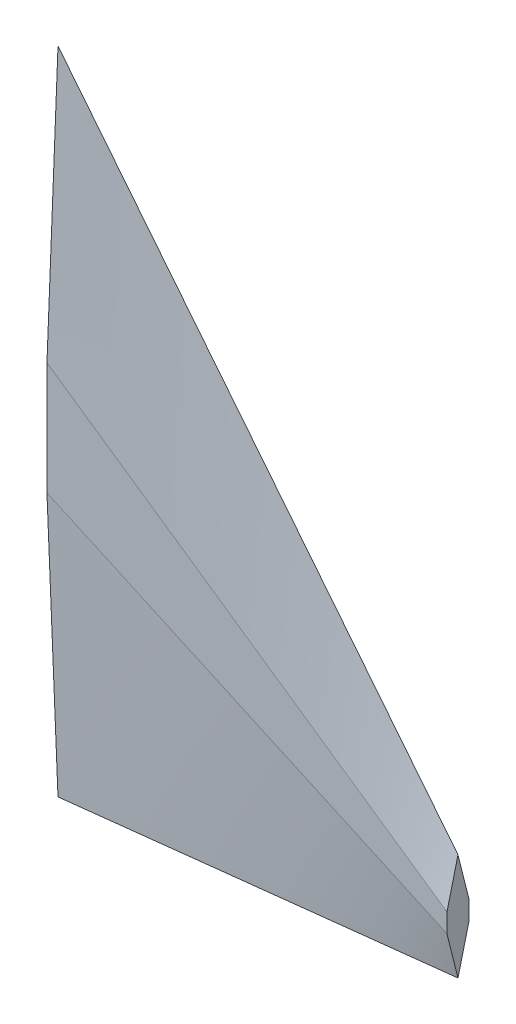
SolidWorks part; units mm, degrees
material "Hexcel AS4C (3000 Filaments)"
ref_plane "Front Plane" through (0, 0, 0) normal (0, 0, 1) x (1, 0, 0)
ref_plane "Top Plane" through (0, 0, 0) normal (0, 1, 0) x (1, 0, 0)
ref_plane "Right Plane" through (0, 0, 0) normal (1, 0, 0) x (0, 0, -1)
sketch "Sketch1" plane through (0, 0, 0) normal (1, 0, 0) x (0, 0, -1)
  line L0 (0, 74.29) -> (2.5212, 12.87)
  line L1 (2.5212, 12.87) -> (2.5212, -12.87)
  line L2 (2.5212, -12.87) -> (0, -74.29)
  line L3 (0, 10.685) -> (0, 13.7664) construction
  line L4 (0, 74.29) -> (0, -74.29) construction
  line L5 (-2.5212, -12.87) -> (0, -74.29)
  line L6 (-2.5212, 12.87) -> (-2.5212, -12.87)
  line L7 (0, 74.29) -> (-2.5212, 12.87)
  point P4 (2.5212, 0)
  point P7 (0, 0)
  dimension "D1" = 25.74
  dimension "D2" = 148.58
ref_plane "Plane1" through (91.39, 0, 0) normal (1, 0, 0) x (0, 0, -1)
sketch "Sketch2" plane through (91.39, 0, 0) normal (1, 0, 0) x (0, 0, -1)
  line L2 (0, -40.04) -> (0, -64.424) construction
  line L8 (0, -64.424) -> (2.5212, -54.391)
  line L9 (0, -199989.315) -> (0, 200013.7664) construction
  line L10 (2.5212, 12.87) -> (2.5212, -12.87) construction
  line L11 (2.5212, -54.391) -> (2.5212, -50.073)
  line L12 (2.5212, -50.073) -> (0, -40.04)
  line L13 (-2.5212, -50.073) -> (0, -40.04)
  line L14 (-2.5212, -54.391) -> (-2.5212, -50.073)
  line L15 (0, -64.424) -> (-2.5212, -54.391)
  point P8 (0, -52.232)
  point P9 (2.5212, -52.232)
  dimension "D1" = 24.384
  dimension "D2" = 4.318
  dimension "D3" = 114.33
loft "Loft1" add profiles "Sketch1", "Sketch2"
